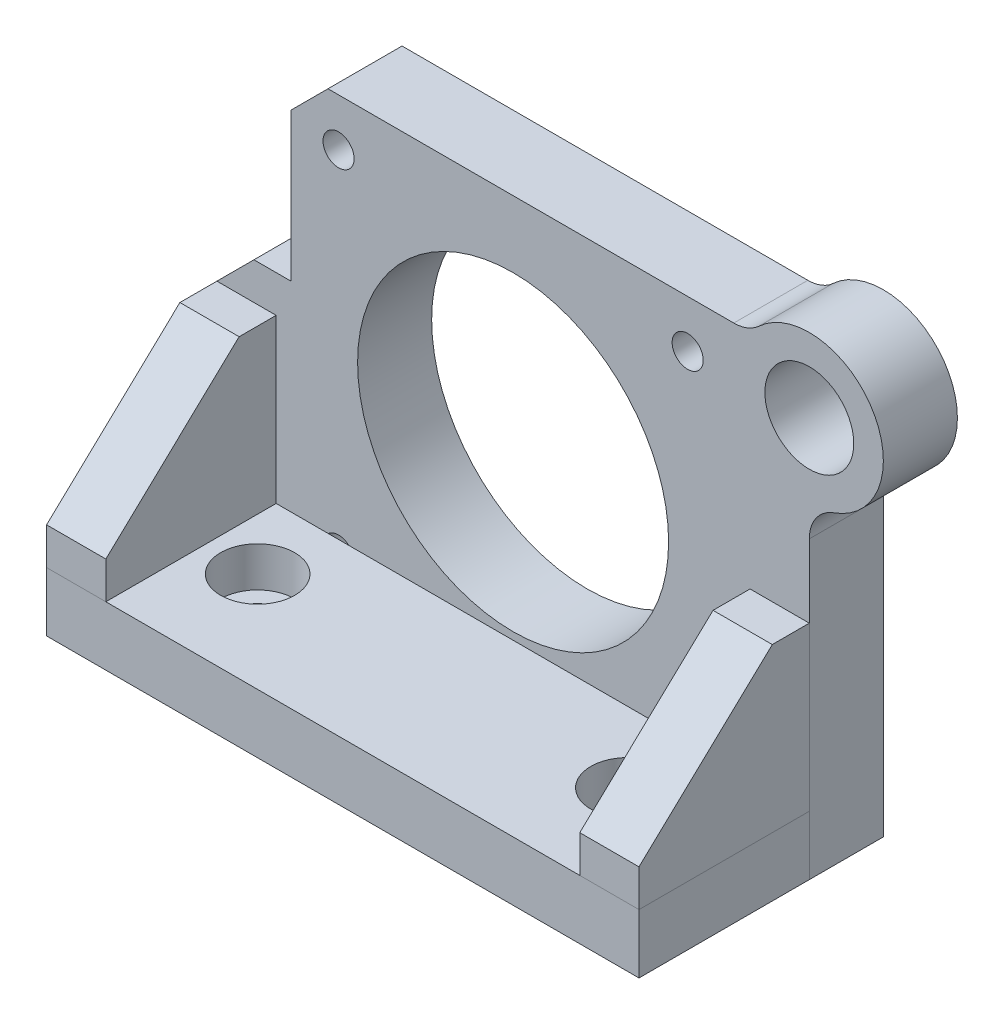
SolidWorks part; units mm, degrees
material "1023 Листовая углеродистая сталь (SS)"
ref_plane "Front" through (0, 0, 0) normal (0, 0, 1) x (1, 0, 0)
ref_plane "Top" through (0, 0, 0) normal (0, 1, 0) x (1, 0, 0)
ref_plane "Right" through (0, 0, 0) normal (1, 0, 0) x (0, 0, -1)
sketch "Sketch1" plane through (0, 0, 0) normal (0, 0, 1) x (1, 0, 0)
  line L1 (-30, 30) -> (32, 30)
  line L2 (-30, 30) -> (-30, 5)
  line L5 (-40, -30) -> (40, -30)
  line L6 (-40, -30) -> (-40, 5)
  line L7 (-40, 5) -> (-30, 5)
  line L8 (40, -30) -> (40, 14)
  circle A0 centre (0, 0) radius 21
  circle A1 centre (40, 24) radius 6
  arc A2 (40, 14) -> (32, 30) centre (40, 24) ccw
  dimension "D1" = 42
  dimension "D4" = 30
  dimension "D9" = 12
  dimension "D10" = 20
  dimension "D2" = 44
  dimension "D3" = 25
  dimension "D5" = 40
  dimension "D6" = 35
  dimension "D7" = 80
  dimension "D8" = 10
extrude "Extrude1" add sketch "Sketch1" along normal blind 10
hole_wizard "M5 Tapped Hole1" positions "Sketch4" profile "Sketch5" tap size "M5" standard "DIN" end condition through all
sketch "Sketch4" plane through (0, 0, 10) normal (0, 0, 1) x (1, 0, 0)
  line L1 (-23.5714, 23.5714) -> (23.5714, 23.5714)
  line L2 (-23.5714, 23.5714) -> (-23.5714, -23.5714)
  line L3 (-23.5714, -23.5714) -> (23.5714, -23.5714)
  line L4 (23.5714, 23.5714) -> (23.5714, -23.5714)
  circle A0 centre (0, 0) radius 33.335
  point P0 (-23.5714, 23.5714)
  point P2 (23.5714, 23.5714)
  point P4 (23.5714, -23.5714)
  point P6 (-23.5714, -23.5714)
  dimension "D1" = 66.67
sketch "Sketch5" plane through (-23.5714, 23.5714, 10) normal (1, 0, 0) x (0, -1, 0)
  line L0 (0, 0) -> (0, 10)
  line L1 (0, 10) -> (2.1, 10)
  line L2 (2.1, 10) -> (2.1, 0)
  line L5 (2.1, 0) -> (0, 0)
  line L11 (0, -6.35) -> (0, 107.95) construction
  dimension "Диаметр проходного сверла" = 4.2
  dimension "Глубина проходного сверла" = 10
cosmetic thread "Cosmetic Thread1" parameters "D2"=5
cosmetic thread "Cosmetic Thread2" parameters "D2"=5
cosmetic thread "Cosmetic Thread3" parameters "D2"=5
cosmetic thread "Cosmetic Thread4" parameters "D2"=5
sketch "Sketch6" plane through (0, -30, 0) normal (0, -1, 0) x (1, 0, 0)
  line L0 (-40, 10) -> (-40, 0) construction
  line L1 (-40, 10) -> (40, 10)
  line L2 (-40, 10) -> (-40, 33)
  line L3 (-40, 33) -> (40, 33)
  line L4 (40, 10) -> (40, 33)
  line L5 (-40, 10) -> (40, 10) construction
  dimension "D1" = 23
  dimension "D2" = 80
extrude "Extrude2" add sketch "Sketch6" against normal blind 8 separate body
chamfer "Chamfer1" distance 5 angle 45 2 edges at (-40, 5, 5) (-30, 30, 5)
sketch "Sketch7" plane through (40, 0, 0) normal (1, 0, 0) x (0, 0, -1)
  line L0 (-10, 0) -> (-15, 0)
  line L1 (-15, 0) -> (-33, -17)
  line L2 (-33, -17) -> (-33, -22)
  line L4 (-33, -22) -> (-33, -30) construction
  line L5 (-33, -22) -> (-10, -22)
  line L6 (-10, -22) -> (-10, 0)
  line L7 (-10, -30) -> (-10, 14) construction
  line L8 (-10, -22) -> (-33, -22) construction
  dimension "D1" = 5
  dimension "D2" = 5
extrude "Extrude3" add sketch "Sketch7" against normal blind 8 separate body
sketch "Sketch8" plane through (-40, 0, 0) normal (-1, 0, 0) x (0, 0, 1)
  line L5 (15, 0) -> (10, 0)
  line L6 (33, -17) -> (15, 0)
  line L7 (33, -22) -> (33, -17)
  line L8 (10, -22) -> (33, -22)
  line L9 (10, 0) -> (10, -22)
  line L10 (15, 0) -> (10, 0)
  line L11 (33, -17) -> (15, 0)
  line L12 (33, -22) -> (33, -17)
  line L13 (10, -22) -> (33, -22)
  line L14 (10, 0) -> (10, -22)
  dimension "D1" = 0
extrude "Extrude4" add sketch "Sketch8" against normal blind 8 separate body
hole_wizard "CBORE for M5 Hex Socket Head Cap Screw1" positions "Sketch11" profile "Sketch10" counterbore size "M5" standard "DIN" end condition through all
sketch "Sketch11" plane through (0, -22, 0) normal (0, -1, 0) x (-1, 0, 0)
  line L1 (-25, -12) -> (25, -12)
  line L2 (-25, -12) -> (-25, -27)
  line L3 (-25, -27) -> (25, -27)
  line L4 (25, -12) -> (25, -27)
  line L5 (-25, -12) -> (25, -27) construction
  line L6 (-25, -27) -> (25, -12) construction
  line L7 (0, 0) -> (0, -12) construction
  line L9 (-40, -33) -> (40, -33) construction
  point P79 (25, -19.5)
  point P81 (-25, -19.5)
  dimension "D1" = 15
  dimension "D2" = 50
  dimension "D3" = 6
sketch "Sketch10" plane through (25, -22, 19.5) normal (1, 0, 0) x (0, 0, 1)
  line L0 (0, 0) -> (0, 8)
  line L1 (0, 8) -> (2.75, 8)
  line L3 (2.75, 8) -> (2.75, 5.4)
  line L4 (2.75, 5.4) -> (5, 5.4)
  line L5 (5, 5.4) -> (5, 0)
  line L7 (5, 0) -> (0, 0)
  line L11 (0, -6.35) -> (0, 107.95) construction
  dimension "Диаметр сквозного отверстия" = 5.5
  dimension "Глубина сквозного отверстия" = 8
  dimension "Диаметр цековки" = 10
  dimension "Глубина цековки" = 5.4
fillet "Fillet1" radius 5 2 edges at (32, 30, 5) (40, 14, 5)
